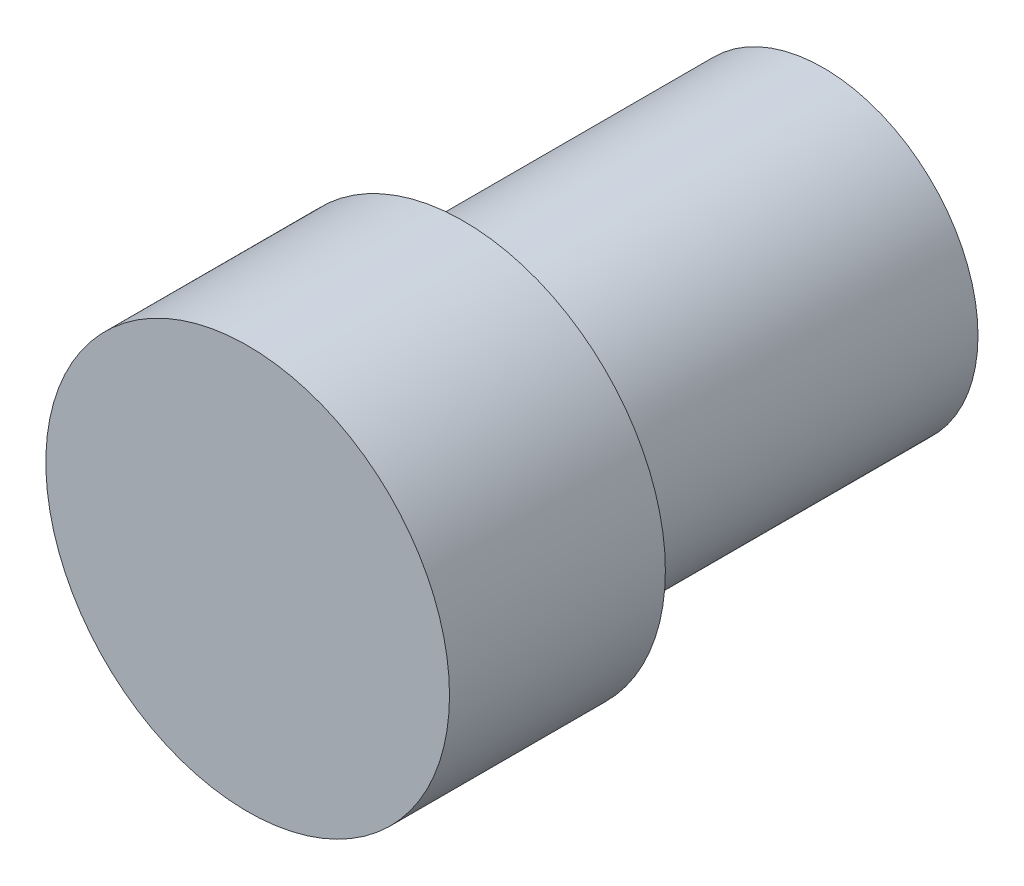
SolidWorks part; units mm, degrees
ref_plane "Front Plane" through (0, 0, 0) normal (0, 0, 1) x (1, 0, 0)
ref_plane "Top Plane" through (0, 0, 0) normal (0, 1, 0) x (1, 0, 0)
ref_plane "Right Plane" through (0, 0, 0) normal (1, 0, 0) x (0, 0, -1)
sketch "Sketch1" plane through (0, 0, 0) normal (0, 0, 1) x (1, 0, 0)
  circle A0 centre (0, 0) radius 5.461
extrude "Extrude1" add sketch "Sketch1" along normal blind 12.7
sketch "Sketch2" plane through (0, 0, 12.7) normal (0, 0, 1) x (1, 0, 0)
  circle A0 centre (0, 0) radius 7.1251
extrude "Extrude2" add sketch "Sketch2" along normal blind 7.62
